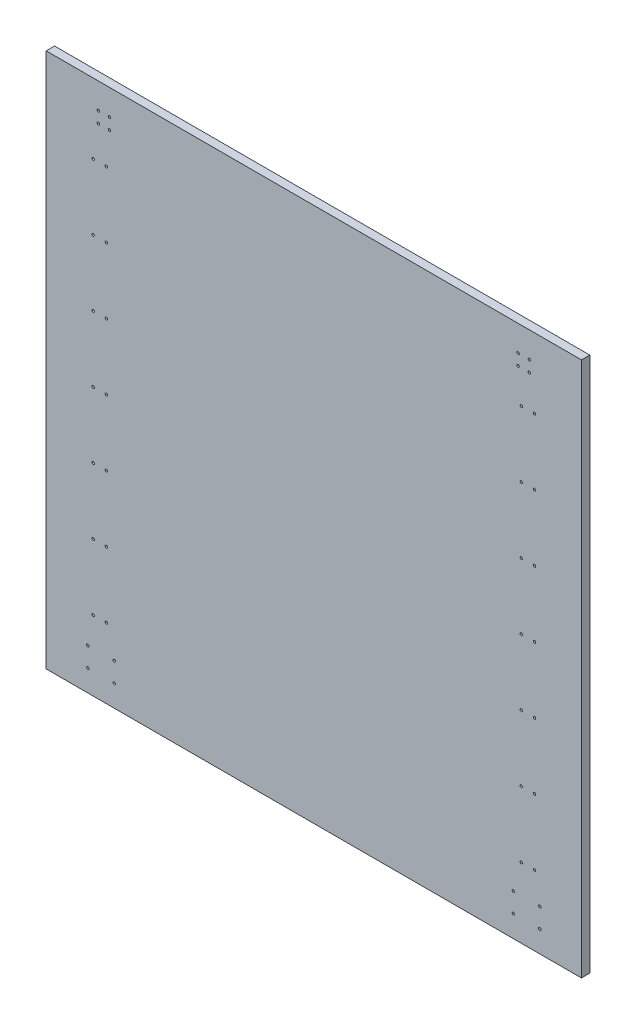
SolidWorks part; units mm, degrees
ref_plane "Front Plane" through (0, 0, 0) normal (0, 0, 1) x (1, 0, 0)
ref_plane "Top Plane" through (0, 0, 0) normal (0, 1, 0) x (1, 0, 0)
ref_plane "Right Plane" through (0, 0, 0) normal (1, 0, 0) x (0, 0, -1)
sketch "Sketch1" plane through (0, 0, 0) normal (0, 0, 1) x (1, 0, 0)
  line L1 (-609.6, -609.6) -> (609.6, -609.6)
  line L2 (-609.6, -609.6) -> (-609.6, 609.6)
  line L3 (-609.6, 609.6) -> (609.6, 609.6)
  line L4 (609.6, -609.6) -> (609.6, 609.6)
  line L5 (-609.6, -609.6) -> (609.6, 609.6) construction
  line L6 (-609.6, 609.6) -> (609.6, -609.6) construction
  point P0 (0, 0)
  dimension "D1" = 1219.2
extrude "Boss-Extrude1" add sketch "Sketch1" along normal blind 19.05
sketch "Sketch2" plane through (0, 0, 0) normal (0, 0, -1) x (-1, 0, 0)
  line L0 (465.3625, 550.8) -> (465.3625, 525.4) construction
  line L1 (465.3625, 525.4) -> (490.7625, 525.4) construction
  point P0 (-490.7625, 550.8)
  point P1 (-465.3625, 550.8)
  point P3 (-465.3625, 525.4)
  point P5 (-490.7625, 525.4)
  point P7 (-472.5625, 450)
  point P9 (-502.5625, 450)
  point P11 (-472.5625, 300)
  point P13 (-502.5625, 300)
  point P15 (-472.5625, 150)
  point P17 (-502.5625, 150)
  point P19 (-472.5625, 0)
  point P21 (-502.5625, 0)
  point P23 (-472.5625, -150)
  point P25 (-502.5625, -150)
  point P27 (-472.5625, -300)
  point P29 (-502.5625, -300)
  point P31 (-472.5625, -450)
  point P33 (-502.5625, -450)
  point P35 (-454.4, -515.875)
  point P37 (-454.4, -560.325)
  point P39 (-514.725, -560.325)
  point P41 (-514.725, -515.875)
  point P43 (514.725, -515.875)
  point P45 (454.4, -515.875)
  point P47 (454.4, -560.325)
  point P49 (514.725, -560.325)
  point P51 (502.5625, -450)
  point P53 (472.5625, -450)
  point P55 (472.5625, -300)
  point P57 (502.5625, -300)
  point P59 (502.5625, -150)
  point P61 (472.5625, -150)
  point P63 (502.5625, 0)
  point P65 (472.5625, 0)
  point P67 (502.5625, 150)
  point P69 (472.5625, 150)
  point P71 (502.5625, 300)
  point P73 (472.5625, 300)
  point P75 (502.5625, 450)
  point P77 (472.5625, 450)
  point P79 (490.7625, 550.8)
  point P81 (490.7625, 525.4)
  point P83 (465.3625, 550.8)
  point P88 (465.3625, 525.4)
  point P90 (0, 0)
  point P91 (0, 0)
  point P92 (0, 0)
hole_wizard "CSK for M5 Flat Head Machine Screw1" positions "Sketch3" profile "Sketch4" countersink size "M5" standard "ANSI Metric" end condition through all
sketch "Sketch3" plane through (0, 0, 0) normal (0, 0, -1) x (-1, 0, 0)
  point P1 (-514.725, -515.875)
  point P3 (-514.725, -560.325)
  point P5 (-454.4, -560.325)
  point P7 (-454.4, -515.875)
  point P9 (-502.5625, -450)
  point P11 (-472.5625, -450)
  point P13 (-502.5625, -300)
  point P15 (-472.5625, -300)
  point P17 (-502.5625, -150)
  point P19 (-472.5625, -150)
  point P21 (-502.5625, 0)
  point P23 (-472.5625, 0)
  point P25 (-502.5625, 150)
  point P27 (-472.5625, 150)
  point P29 (-502.5625, 300)
  point P31 (-472.5625, 300)
  point P33 (-502.5625, 450)
  point P35 (-472.5625, 450)
  point P37 (-490.7625, 525.4)
  point P39 (-490.7625, 550.8)
  point P41 (-465.3625, 550.8)
  point P43 (-465.3625, 525.4)
  point P45 (465.3625, 525.4)
  point P49 (472.5625, 150)
  point P51 (502.5625, 150)
  point P53 (472.5625, 300)
  point P55 (502.5625, 300)
  point P57 (472.5625, 450)
  point P59 (502.5625, 450)
  point P61 (490.7625, 525.4)
  point P63 (490.7625, 550.8)
  point P65 (465.3625, 550.8)
  point P67 (454.4, -515.875)
  point P69 (454.4, -560.325)
  point P71 (514.725, -560.325)
  point P73 (514.725, -515.875)
  point P75 (472.5625, -450)
  point P77 (502.5625, -450)
  point P79 (472.5625, -300)
  point P81 (502.5625, -300)
  point P83 (472.5625, -150)
  point P85 (502.5625, -150)
  point P87 (472.5625, 0)
  point P89 (502.5625, 0)
sketch "Sketch4" plane through (514.725, -515.875, 0) normal (1, 0, 0) x (0, 1, 0)
  line L0 (0, 0) -> (0, 19.05)
  line L1 (0, 19.05) -> (2.75, 19.05)
  line L2 (2.75, 19.05) -> (2.75, 2.45)
  line L3 (2.75, 2.45) -> (5.2, 0)
  line L5 (5.2, 0) -> (0, 0)
  line L6 (-2.75, 2.45) -> (-5.2, 0) construction
  line L11 (0, -6.35) -> (0, 107.95) construction
  dimension "Thru Hole Dia." = 5.5
  dimension "Thru Hole Depth" = 19.05
  dimension "Near C'Sink Dia." = 10.4
  dimension "Near C'Sink Angle" = 90
